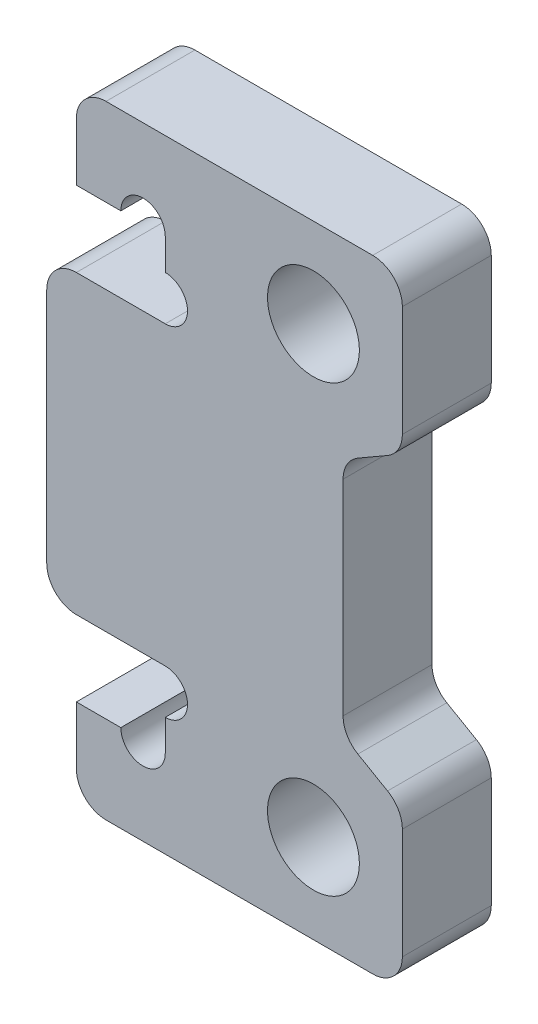
SolidWorks part; units mm, degrees
ref_plane "前视基准面" through (0, 0, 0) normal (0, 0, 1) x (1, 0, 0)
ref_plane "上视基准面" through (0, 0, 0) normal (0, 1, 0) x (1, 0, 0)
ref_plane "右视基准面" through (0, 0, 0) normal (1, 0, 0) x (0, 0, -1)
sketch "草图1" plane through (0, 0, 0) normal (0, 0, 1) x (1, 0, 0)
  line L0 (0, -7.5) -> (0, 7.5) construction
  line L1 (-5, 10.5) -> (-5, -10.5)
  line L2 (-5, 10.5) -> (3, 10.5)
  line L3 (3, 10.5) -> (3, 5.1906)
  line L4 (3, 5.1906) -> (1, 4.0359)
  line L5 (1, 4.0359) -> (1, -4.0359)
  line L6 (1, -4.0359) -> (3, -5.1906)
  line L7 (3, -5.1906) -> (3, -10.5)
  line L8 (3, -10.5) -> (-5, -10.5)
  circle A1 centre (0, 7.5) radius 1.55
  circle A2 centre (0, -7.5) radius 1.55
  point P5 (0, 0)
  dimension "D1" = 15
  dimension "D2" = 3.1
  dimension "D4" = 3
  dimension "D9" = 3
  dimension "D3" = 5
  dimension "D5" = 2
  dimension "D6" = 60
  dimension "D7" = 3.5
  dimension "D8" = 3.5
  dimension "D10" = 3
extrude "凸台-拉伸1" add sketch "草图1" along normal mid plane 3
sketch "草图2" plane through (0, 0, 1.5) normal (0, 0, 1) x (1, 0, 0)
  line L5 (-5, 10.5) -> (-5, -10.5) construction
  line L7 (-5, -7.55) -> (-8, -7.55)
  line L8 (-8, -7.55) -> (-8, -10.5)
  line L9 (-8, -10.5) -> (-5, -10.5)
  line L10 (-5, -10.5) -> (-5, -7.55)
  line L11 (-5, 5) -> (-9, 5)
  line L12 (-9, 5) -> (-9, -5)
  line L13 (-9, -5) -> (-5, -5)
  line L14 (-5, -5) -> (-5, 5)
  line L15 (-5, 10.5) -> (-8, 10.5)
  line L16 (-8, 10.5) -> (-8, 7.55)
  line L17 (-8, 7.55) -> (-5, 7.55)
  line L18 (-5, 7.55) -> (-5, 10.5)
  point P18 (-5, 0)
  dimension "D1" = 10
  dimension "D2" = 3
  dimension "D3" = 4
  dimension "D4" = 15.1
extrude "凸台-拉伸2" add sketch "草图2" against normal up to surface (3 mm away) up to face at (1.55, 7.5, -1.5)
sketch "草图3" plane through (0, 0, 1.5) normal (0, 0, 1) x (1, 0, 0)
  line L0 (-8, 7.55) -> (-5, 7.55) construction
  line L1 (-5, 7.55) -> (-5, 5) construction
  line L2 (-5, -5) -> (-5, -7.55) construction
  line L3 (-5, -7.55) -> (-8, -7.55) construction
  circle A0 centre (-5.75, 7.55) radius 0.75
  circle A1 centre (-5, 5.75) radius 0.75
  circle A2 centre (-5, -5.75) radius 0.75
  circle A3 centre (-5.75, -7.55) radius 0.75
  dimension "D1" = 1.5
extrude "切除-拉伸1" cut sketch "草图3" against normal through all
fillet "圆角1" radius 1 10 edges at (3, 5.1906, 0) (3, -5.1906, 0) (3, -10.5, 0) (3, 10.5, 0) (1, -4.0359, 0) (1, 4.0359, 0) (-8, 10.5, 0) (-8, -10.5, 0) (-9, -5, 0) (-9, 5, 0)
